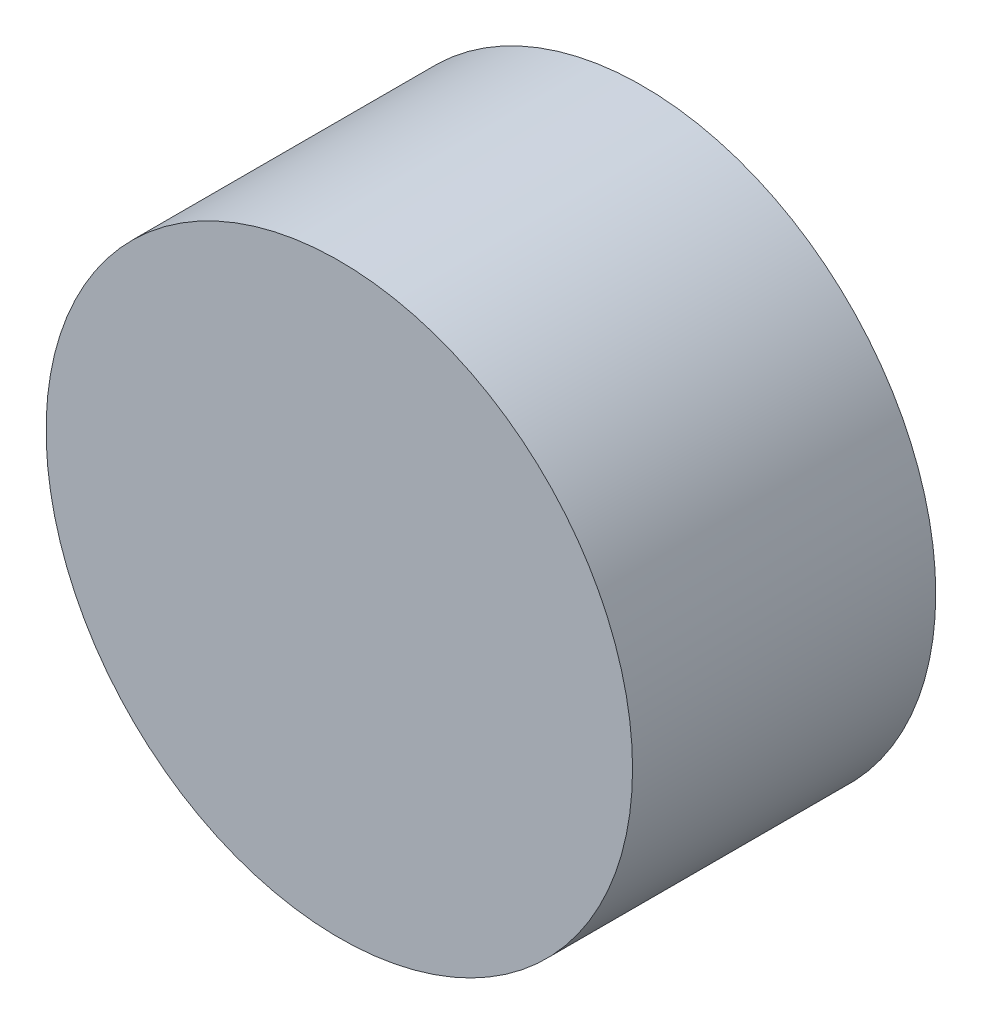
SolidWorks part; units mm, degrees
ref_plane "Front Plane" through (0, 0, 0) normal (0, 0, 1) x (1, 0, 0)
ref_plane "Top Plane" through (0, 0, 0) normal (0, 1, 0) x (1, 0, 0)
ref_plane "Right Plane" through (0, 0, 0) normal (1, 0, 0) x (0, 0, -1)
sketch "Sketch1" plane through (0, 0, 0) normal (0, 0, 1) x (1, 0, 0)
  circle A0 centre (0, 0) radius 14.75
  dimension "D1" = 29.5
extrude "Boss-Extrude1" add sketch "Sketch1" along normal blind 15.25
